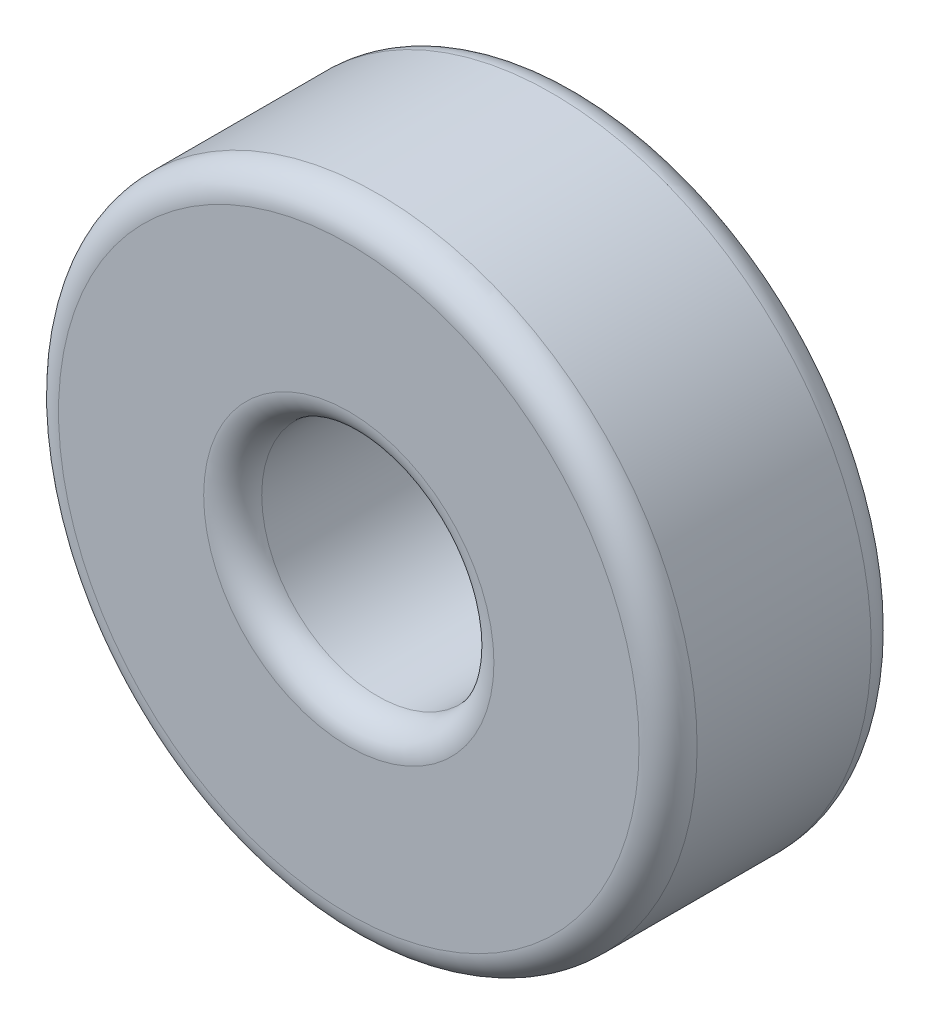
SolidWorks part; units mm, degrees
ref_plane "Plane1" through (0, 0, 0) normal (0, 0, 1) x (1, 0, 0)
ref_plane "Plane2" through (0, 0, 0) normal (0, 1, 0) x (1, 0, 0)
ref_plane "Plane3" through (0, 0, 0) normal (1, 0, 0) x (0, 0, -1)
sketch "Esquisse1" plane through (0, 0, 0) normal (0, 0, 1) x (1, 0, 0)
  circle A0 centre (0, 0) radius 5.5
  circle A1 centre (0, 0) radius 2
  dimension "D1" = 11
  dimension "D2" = 4
extrude "Base-Extrusion" add sketch "Esquisse1" along normal blind 4
fillet "Congé1" radius 0.5
